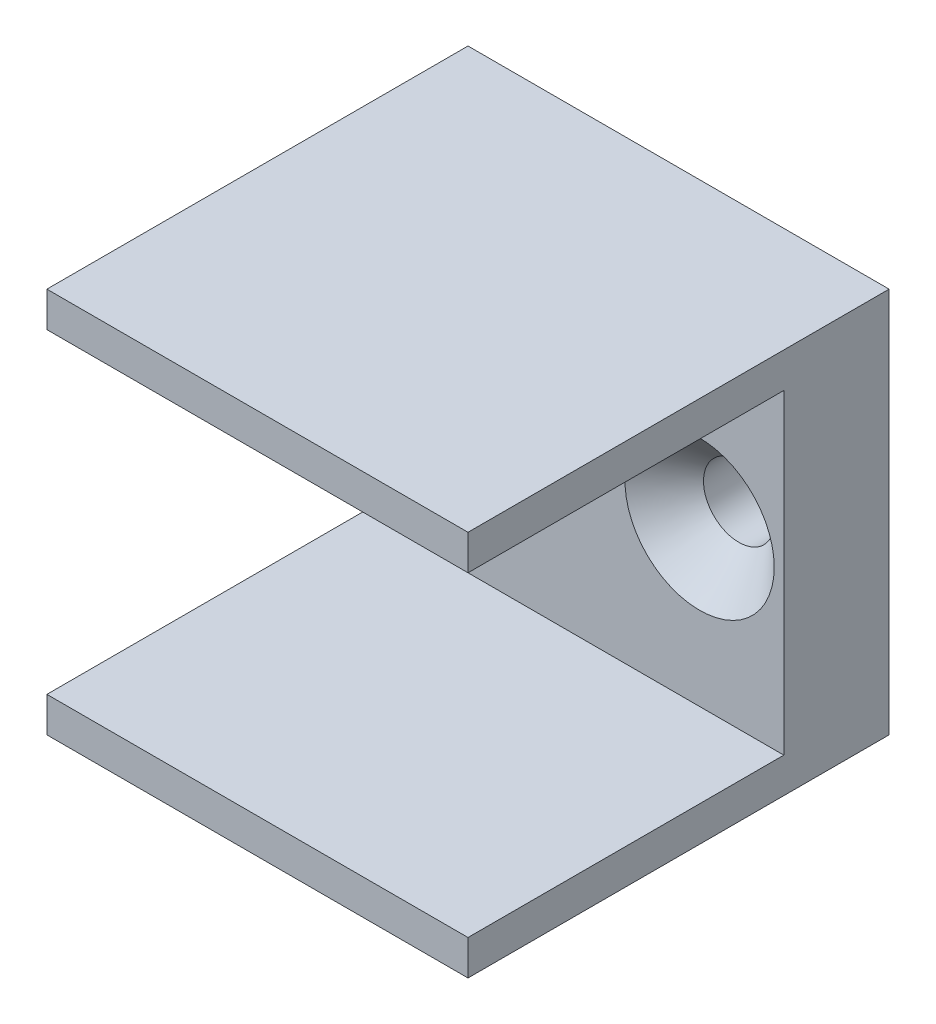
SolidWorks part; units mm, degrees
material "ALUMINUM 6061-T6"
ref_plane "Front Plane" through (0, 0, 0) normal (0, 0, 1) x (1, 0, 0)
ref_plane "Top Plane" through (0, 0, 0) normal (0, 1, 0) x (1, 0, 0)
ref_plane "Right Plane" through (0, 0, 0) normal (1, 0, 0) x (0, 0, -1)
sketch "Sketch1" plane through (0, 0, 0) normal (0, 0, 1) x (1, 0, 0)
  line L1 (-19.05, -17.4625) -> (19.05, -17.4625)
  line L2 (-19.05, -17.4625) -> (-19.05, 17.4625)
  line L3 (-19.05, 17.4625) -> (19.05, 17.4625)
  line L4 (19.05, -17.4625) -> (19.05, 17.4625)
  line L5 (-19.05, -17.4625) -> (19.05, 17.4625) construction
  line L6 (-19.05, 17.4625) -> (19.05, -17.4625) construction
  point P0 (0, 0)
  dimension "D1" = 38.1
  dimension "D2" = 34.925
extrude "Boss-Extrude1" add sketch "Sketch1" along normal mid plane 38.1
sketch "Sketch3" plane through (0, 0, 19.05) normal (0, 0, 1) x (1, 0, 0)
  line L0 (-19.05, 17.4625) -> (-19.05, -17.4625) construction
  line L1 (-19.05, 14.2875) -> (19.05, 14.2875)
  line L2 (-19.05, 14.2875) -> (-19.05, -14.2875)
  line L3 (-19.05, -14.2875) -> (19.05, -14.2875)
  line L4 (19.05, 14.2875) -> (19.05, -14.2875)
  line L5 (19.05, -17.4625) -> (19.05, 17.4625) construction
  line L6 (19.05, 17.4625) -> (-19.05, 17.4625) construction
  line L7 (-19.05, -17.4625) -> (19.05, -17.4625) construction
  dimension "D1" = 3.175
  dimension "D2" = 3.175
extrude "Cut-Extrude1" cut sketch "Sketch3" against normal blind 28.575
hole_wizard "CSK for M6 Hex Socket Countersunk Head Screw1" positions "Sketch5" profile "Sketch4" countersink size "M6" standard "Lanco STD" end condition through all
sketch "Sketch5" plane through (0, 0, -9.525) normal (0, 0, 1) x (1, 0, 0)
  line L0 (-19.05, 14.2875) -> (-19.05, -14.2875) construction
  line L1 (19.05, -14.2875) -> (19.05, 14.2875) construction
  point P0 (-11.43, 0)
  point P2 (11.43, 0)
  point P10 (19.05, 0)
  dimension "D1" = 7.62
  dimension "D2" = 7.62
sketch "Sketch4" plane through (-11.43, 0, -9.525) normal (1, 0, 0) x (0, -1, 0)
  line L0 (0, 0) -> (0, 9.525)
  line L1 (0, 9.525) -> (3.2, 9.525)
  line L2 (3.2, 9.525) -> (3.2, 3.55)
  line L3 (3.2, 3.55) -> (6.75, 0)
  line L5 (6.75, 0) -> (0, 0)
  line L6 (-3.2, 3.55) -> (-6.75, 0) construction
  line L11 (0, -6.35) -> (0, 107.95) construction
  dimension "Thru Hole Dia." = 6.4
  dimension "Thru Hole Depth" = 9.525
  dimension "Near C'Sink Dia." = 13.5
  dimension "Near C'Sink Angle" = 90
